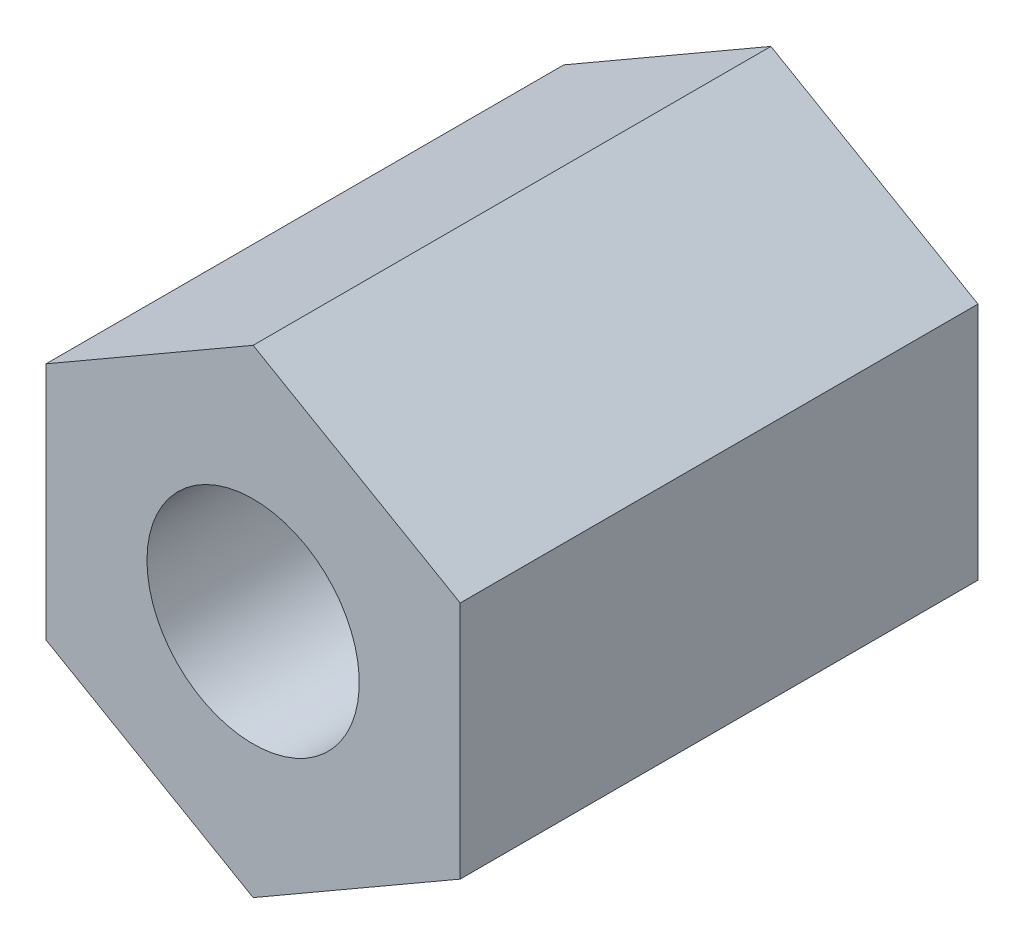
SolidWorks part; units mm, degrees
material "POM Acetal Copolymer"
ref_plane "Front Plane" through (0, 0, 0) normal (0, 0, 1) x (1, 0, 0)
ref_plane "Top Plane" through (0, 0, 0) normal (0, 1, 0) x (1, 0, 0)
ref_plane "Right Plane" through (0, 0, 0) normal (1, 0, 0) x (0, 0, -1)
sketch "Sketch1" plane through (0, 0, 0) normal (0, 0, 1) x (1, 0, 0)
  line L1 (0, -2.3094) -> (2, -1.1547)
  line L2 (2, -1.1547) -> (2, 1.1547)
  line L3 (2, 1.1547) -> (0, 2.3094)
  line L4 (0, 2.3094) -> (-2, 1.1547)
  line L5 (-2, 1.1547) -> (-2, -1.1547)
  line L6 (-2, -1.1547) -> (0, -2.3094)
  circle A0 centre (0, 0) radius 2 construction
  dimension "D1" = 4
extrude "Boss-Extrude1" add sketch "Sketch1" along normal blind 5
hole_wizard "Trou pour taraudage pour trou taraudé M2.51" positions "Esquisse10" profile "Esquisse9" hole size "M2.5" standard "ISO" end condition through all
sketch "Esquisse10" plane through (0, 0, 0) normal (0, 0, -1) x (-1, 0, 0)
  point P0 (0, 0)
sketch "Esquisse9" plane through (0, 0, 0) normal (1, 0, 0) x (0, 1, 0)
  line L0 (0, 0) -> (0, 5)
  line L1 (0, 5) -> (1.025, 5)
  line L2 (1.025, 5) -> (1.025, 0)
  line L5 (1.025, 0) -> (0, 0)
  line L11 (0, -6.35) -> (0, 107.95) construction
  dimension "Diamètre du perçage jusqu'au prochain" = 2.05
  dimension "Profondeur du perçage jusqu'au prochain" = 5
